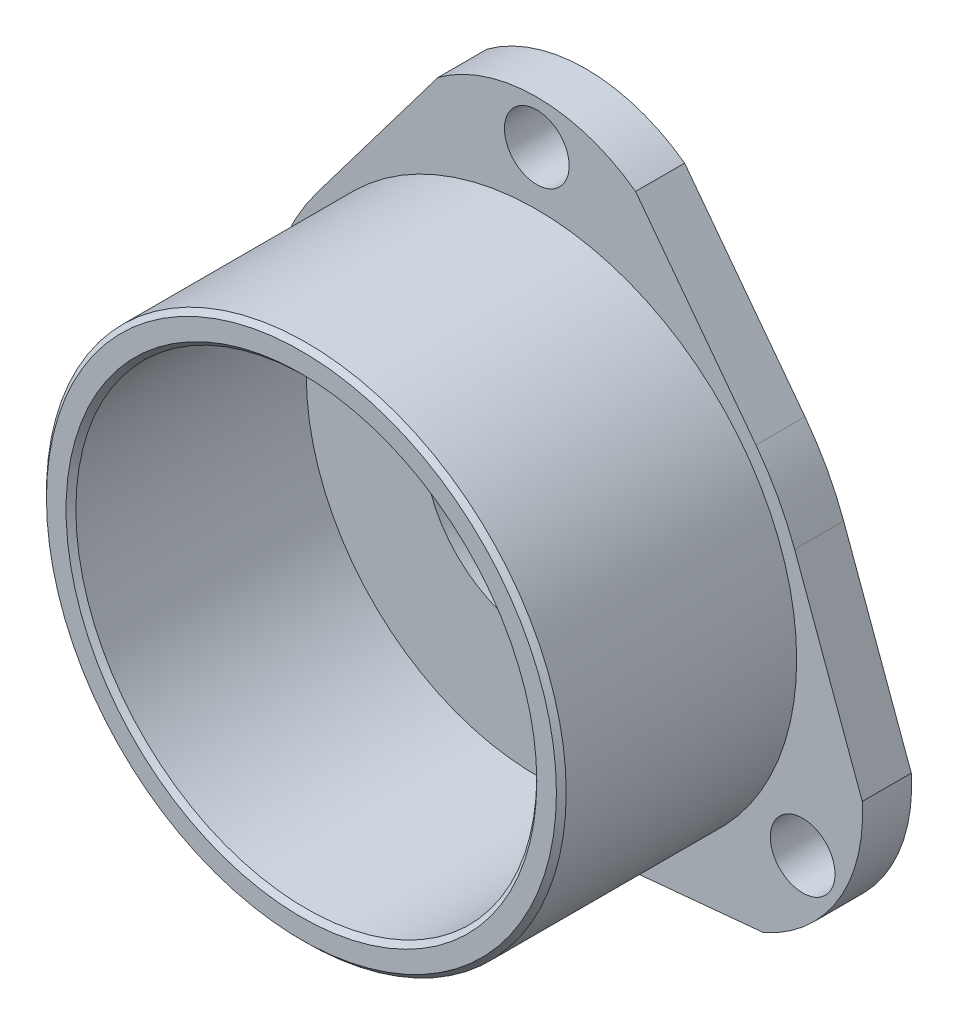
SolidWorks part; units mm, degrees
material "Lega 1060"
ref_plane "Piano frontale" through (0, 0, 0) normal (0, 0, 1) x (1, 0, 0)
ref_plane "Piano superiore" through (0, 0, 0) normal (0, 1, 0) x (1, 0, 0)
ref_plane "Piano destro" through (0, 0, 0) normal (1, 0, 0) x (0, 0, -1)
sketch "Schizzo1" plane through (0, 0, 0) normal (0, 0, 1) x (1, 0, 0)
  line L0 (2.4886, -39.5016) -> (20.3197, -37.8035)
  line L1 (30.3913, -21.1871) -> (23.4933, -2.3684)
  line L2 (19.5483, 4.8688) -> (7.2754, 21.1211)
  line L3 (-12.8679, 21.1211) -> (-25.1408, 4.8688)
  line L4 (-29.0858, -2.3684) -> (-35.9838, -21.1871)
  line L5 (-25.9122, -37.8035) -> (-8.0811, -39.5016)
  arc A2 (-8.0811, -39.5016) -> (2.4886, -39.5016) centre (-2.7962, -12.0048) ccw
  arc A3 (20.3197, -37.8035) -> (30.3913, -21.1871) centre (13.4255, -22.2643) ccw
  arc A4 (23.4933, -2.3684) -> (19.5483, 4.8688) centre (-2.7962, -12.0048) ccw
  arc A5 (7.2754, 21.1211) -> (-12.8679, 21.1211) centre (-2.7962, 7.4257) ccw
  arc A6 (-25.1408, 4.8688) -> (-29.0858, -2.3684) centre (-2.7962, -12.0048) ccw
  arc A7 (-35.9838, -21.1871) -> (-25.9122, -37.8035) centre (-19.018, -22.2643) ccw
  point P27 (-2.7962, 19.9952)
  point P28 (24.3146, -29.0048)
  point P29 (-29.9071, -29.0048)
extrude "Estrusione-Estrusione1" add sketch "Schizzo1" along normal blind 5
hole_wizard "Foro per Vite M6-1" positions "Schizzo2" profile "Schizzo3" hole size "M6" standard "ISO" end condition through all
sketch "Schizzo2" plane through (0, 0, 0) normal (0, 0, -1) x (-1, 0, 0)
  point P0 (2.7962, 19.9952)
  point P3 (29.9071, -29.0048)
  point P6 (-24.3146, -29.0048)
sketch "Schizzo3" plane through (-2.7962, 19.9952, 0) normal (1, 0, 0) x (0, 1, 0)
  line L0 (0, 0) -> (0, 5)
  line L1 (0, 5) -> (3.3, 5)
  line L2 (3.3, 5) -> (3.3, 0.025)
  line L3 (3.3, 0.025) -> (3.325, 0)
  line L5 (3.325, 0) -> (0, 0)
  line L6 (-3.3, 0.025) -> (-3.325, 0) construction
  line L11 (0, -6.35) -> (0, 107.95) construction
  dimension "Thru Hole Dia." = 6.6
  dimension "Thru Hole Depth" = 5
  dimension "Near C'Sink Dia." = 6.65
  dimension "Near C'Sink Angle" = 90
sketch "Schizzo4" plane through (0, 0, 5) normal (0, 0, 1) x (1, 0, 0)
  circle A0 centre (-2.7962, -12.0048) radius 26.5
  circle A2 centre (-2.7962, -12.0048) radius 23.5
  dimension "D1" = 53
  dimension "D2" = 47
extrude "Estrusione-Estrusione2" add sketch "Schizzo4" along normal blind 24
sketch "Schizzo5" plane through (0, 0, 0) normal (0, 0, -1) x (-1, 0, 0)
  circle A0 centre (2.7962, -12.0048) radius 11.5
  dimension "D1" = 23
extrude "Taglio-Estrusione1" cut sketch "Schizzo5" against normal up to surface (5 mm away) up to face at (20.7038, -12.0048, 5)
chamfer "Smusso1" distance 0.5 angle 45 2 edges at (20.7038, -12.0048, 29) (23.7038, -12.0048, 29)
